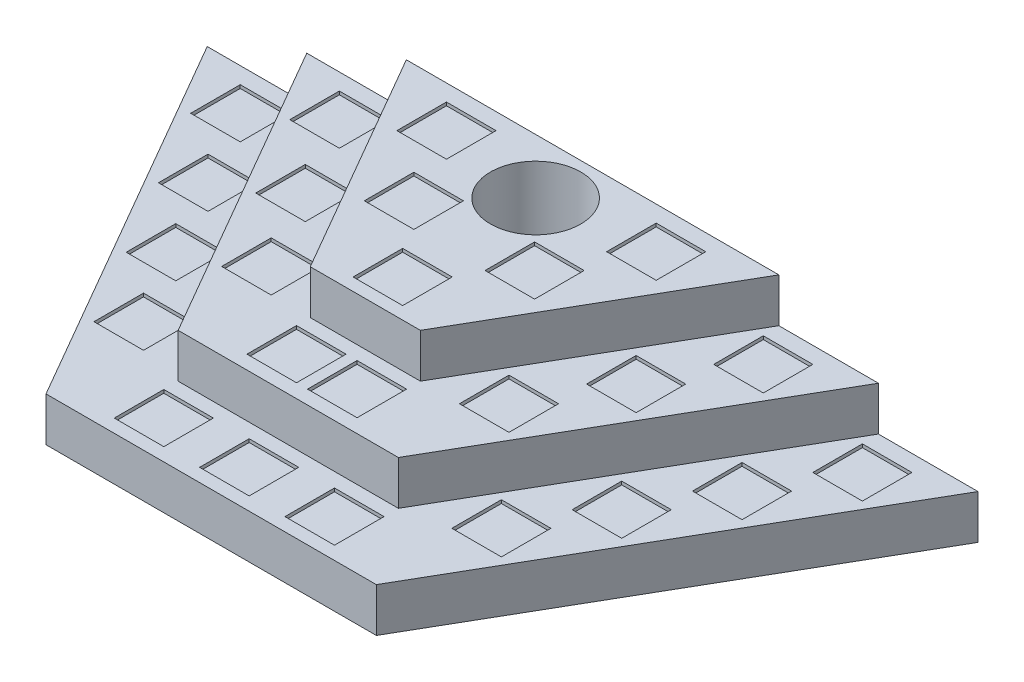
SolidWorks part; units mm, degrees
ref_plane "Front Plane" through (0, 0, 0) normal (0, 0, 1) x (1, 0, 0)
ref_plane "Top Plane" through (0, 0, 0) normal (0, 1, 0) x (1, 0, 0)
ref_plane "Right Plane" through (0, 0, 0) normal (1, 0, 0) x (0, 0, -1)
sketch "Sketch1" plane through (0, 0, 0) normal (0, 1, 0) x (1, 0, 0)
  line L0 (-150, 0) -> (150, 0)
  line L1 (150, 0) -> (350, 346.4102)
  line L2 (350, 346.4102) -> (-350, 346.4102)
  line L3 (-350, 346.4102) -> (-150, 0)
  point P4 (0, 0)
  dimension "D1" = 700
  dimension "D2" = 300
  dimension "D3" = 60
  dimension "D4" = 60
extrude "Boss-Extrude1" add sketch "Sketch1" along normal blind 40
sketch "Sketch3" plane through (0, 40, 0) normal (0, 1, 0) x (1, 0, 0)
  line L0 (-100, 70) -> (100, 70)
  line L1 (-150, 0) -> (150, 0) construction
  line L2 (-100, 70) -> (-259.5855, 346.4102)
  line L3 (350, 346.4102) -> (-350, 346.4102) construction
  line L4 (0, 0) -> (0, 370.2968) construction
  line L5 (100, 70) -> (259.5855, 346.4102)
  line L6 (-50, 140) -> (50, 140)
  line L7 (-50, 140) -> (-169.171, 346.4102)
  line L8 (50, 140) -> (169.171, 346.4102)
  line L9 (-259.5855, 346.4102) -> (-169.171, 346.4102)
  line L10 (259.5855, 346.4102) -> (169.171, 346.4102)
  point P5 (0, 70)
  point P14 (0, 140)
  dimension "D1" = 200
  dimension "D2" = 70
  dimension "D3" = 60
  dimension "D4" = 70
  dimension "D5" = 60
  dimension "D6" = 100
extrude "Boss-Extrude2" add sketch "Sketch3" along normal blind 40
sketch "Sketch4" plane through (0, 40, 0) normal (0, 1, 0) x (1, 0, 0)
  line L17 (-259.5855, 346.4102) -> (-100, 70)
  line L18 (-100, 70) -> (100, 70)
  line L19 (100, 70) -> (259.5855, 346.4102)
  line L20 (259.5855, 346.4102) -> (169.171, 346.4102)
  line L21 (169.171, 346.4102) -> (50, 140)
  line L22 (50, 140) -> (-50, 140)
  line L23 (-50, 140) -> (-169.171, 346.4102)
  line L24 (-169.171, 346.4102) -> (-259.5855, 346.4102)
  line L25 (-259.5855, 346.4102) -> (-100, 70)
  line L26 (-100, 70) -> (100, 70)
  line L27 (100, 70) -> (259.5855, 346.4102)
  line L28 (259.5855, 346.4102) -> (169.171, 346.4102)
  line L32 (169.171, 346.4102) -> (-259.5855, 346.4102)
  dimension "D2" = 0
extrude "Boss-Extrude3" add sketch "Sketch4" along normal blind 80
sketch "Sketch7" plane through (0, 40, 0) normal (0, 1, 0) x (1, 0, 0)
  line L0 (-150, 0) -> (150, 0) construction
  line L1 (-305, 331.4102) -> (-260, 331.4102)
  line L2 (-305, 331.4102) -> (-305, 286.4102)
  line L3 (-305, 286.4102) -> (-260, 286.4102)
  line L4 (-260, 331.4102) -> (-260, 286.4102)
  line L5 (-100, 57) -> (-55, 57)
  line L6 (-100, 57) -> (-100, 12)
  line L7 (-100, 12) -> (-55, 12)
  line L8 (-55, 57) -> (-55, 12)
  line L9 (-259.5855, 346.4102) -> (-350, 346.4102) construction
  line L10 (0, 0) -> (0, 441.8667) construction
  line L11 (-265, 262.1281) -> (-265, 217.1281)
  line L12 (-265, 262.1281) -> (-220, 262.1281)
  line L13 (-220, 262.1281) -> (-220, 217.1281)
  line L14 (-265, 217.1281) -> (-220, 217.1281)
  line L15 (-225, 192.8461) -> (-225, 147.8461)
  line L16 (-225, 192.8461) -> (-180, 192.8461)
  line L17 (-180, 192.8461) -> (-180, 147.8461)
  line L18 (-225, 147.8461) -> (-180, 147.8461)
  line L19 (-185, 123.5641) -> (-185, 78.5641)
  line L20 (-185, 123.5641) -> (-140, 123.5641)
  line L21 (-140, 123.5641) -> (-140, 78.5641)
  line L22 (-185, 78.5641) -> (-140, 78.5641)
  line L23 (305, 286.4102) -> (260, 286.4102)
  line L24 (260, 331.4102) -> (260, 286.4102)
  line L25 (305, 331.4102) -> (260, 331.4102)
  line L26 (305, 331.4102) -> (305, 286.4102)
  line L27 (185, 123.5641) -> (140, 123.5641)
  line L28 (140, 123.5641) -> (140, 78.5641)
  line L29 (185, 78.5641) -> (140, 78.5641)
  line L30 (185, 123.5641) -> (185, 78.5641)
  line L31 (225, 192.8461) -> (180, 192.8461)
  line L32 (180, 192.8461) -> (180, 147.8461)
  line L33 (225, 147.8461) -> (180, 147.8461)
  line L34 (225, 192.8461) -> (225, 147.8461)
  line L35 (265, 262.1281) -> (220, 262.1281)
  line L36 (220, 262.1281) -> (220, 217.1281)
  line L37 (265, 217.1281) -> (220, 217.1281)
  line L38 (265, 262.1281) -> (265, 217.1281)
  line L40 (-22.5, 57) -> (-22.5, 12)
  line L41 (-22.5, 57) -> (22.5, 57)
  line L42 (22.5, 57) -> (22.5, 12)
  line L43 (-22.5, 12) -> (22.5, 12)
  line L44 (55, 57) -> (55, 12)
  line L45 (55, 57) -> (100, 57)
  line L46 (100, 57) -> (100, 12)
  line L47 (55, 12) -> (100, 12)
  point P8 (-220, 239.6281)
  point P47 (0, 12)
  dimension "D1" = 45
  dimension "D2" = 45
  dimension "D3" = 60
  dimension "D4" = 260
  dimension "D6" = 220
  dimension "D7" = 12
  dimension "D8" = 100
  dimension "D5" = 4
  dimension "D9" = 3
extrude "Cut-Extrude2" cut sketch "Sketch7" against normal blind 3
sketch "Sketch8" plane through (0, 80, 0) normal (0, 1, 0) x (1, 0, 0)
  line L0 (-260, 331.4102) -> (-305, 331.4102) construction
  line L1 (-215, 331.4102) -> (-170, 331.4102)
  line L2 (-215, 331.4102) -> (-215, 286.4102)
  line L3 (-215, 286.4102) -> (-170, 286.4102)
  line L4 (-170, 331.4102) -> (-170, 286.4102)
  line L5 (-260, 331.4102) -> (-305, 331.4102) construction
  line L6 (0, 0) -> (0, 453.8323) construction
  line L7 (-172.735, 258.2051) -> (-172.735, 213.2051)
  line L8 (-172.735, 258.2051) -> (-127.735, 258.2051)
  line L9 (-127.735, 258.2051) -> (-127.735, 213.2051)
  line L10 (-172.735, 213.2051) -> (-127.735, 213.2051)
  line L11 (-130.4701, 185) -> (-130.4701, 140)
  line L12 (-130.4701, 185) -> (-85.4701, 185)
  line L13 (-85.4701, 185) -> (-85.4701, 140)
  line L14 (-130.4701, 140) -> (-85.4701, 140)
  line L15 (50, 140) -> (-50, 140) construction
  line L16 (215, 286.4102) -> (170, 286.4102)
  line L17 (170, 331.4102) -> (170, 286.4102)
  line L18 (215, 331.4102) -> (170, 331.4102)
  line L19 (215, 331.4102) -> (215, 286.4102)
  line L20 (172.735, 258.2051) -> (127.735, 258.2051)
  line L21 (127.735, 258.2051) -> (127.735, 213.2051)
  line L22 (172.735, 213.2051) -> (127.735, 213.2051)
  line L23 (172.735, 258.2051) -> (172.735, 213.2051)
  line L24 (130.4701, 185) -> (85.4701, 185)
  line L25 (85.4701, 185) -> (85.4701, 140)
  line L26 (130.4701, 140) -> (85.4701, 140)
  line L27 (130.4701, 185) -> (130.4701, 140)
  dimension "D1" = 170
  dimension "D2" = 3
extrude "Cut-Extrude3" cut sketch "Sketch8" against normal blind 3
sketch "Sketch9" plane through (0, 80, 0) normal (0, 1, 0) x (1, 0, 0)
  line L0 (-130.4701, 140) -> (-85.4701, 140) construction
  line L1 (-50, 127.5) -> (-5, 127.5)
  line L2 (-50, 127.5) -> (-50, 82.5)
  line L3 (-50, 82.5) -> (-5, 82.5)
  line L4 (-5, 127.5) -> (-5, 82.5)
  line L5 (50, 140) -> (-50, 140) construction
  line L7 (5, 127.5) -> (5, 82.5)
  line L8 (5, 127.5) -> (50, 127.5)
  line L9 (50, 127.5) -> (50, 82.5)
  line L10 (5, 82.5) -> (50, 82.5)
  dimension "D1" = 12.5
  dimension "D2" = 2
extrude "Cut-Extrude4" cut sketch "Sketch9" against normal blind 3
sketch "Sketch11" plane through (0, 120, 0) normal (0, 1, 0) x (1, 0, 0)
  line L0 (0, 0) -> (0, 385.805) construction
  line L1 (-77.3205, 261.4102) -> (-77.3205, 216.4102)
  line L2 (-117.735, 331.4102) -> (-72.735, 331.4102)
  line L3 (-117.735, 331.4102) -> (-117.735, 286.4102)
  line L4 (-117.735, 286.4102) -> (-72.735, 286.4102)
  line L5 (-72.735, 331.4102) -> (-72.735, 286.4102)
  line L6 (-77.3205, 261.4102) -> (-32.3205, 261.4102)
  line L7 (-32.3205, 261.4102) -> (-32.3205, 216.4102)
  line L8 (-77.3205, 216.4102) -> (-32.3205, 216.4102)
  line L9 (77.3205, 261.4102) -> (32.3205, 261.4102)
  line L10 (-170, 331.4102) -> (-215, 331.4102) construction
  line L11 (32.3205, 261.4102) -> (32.3205, 216.4102)
  line L12 (77.3205, 216.4102) -> (32.3205, 216.4102)
  line L13 (77.3205, 261.4102) -> (77.3205, 216.4102)
  line L14 (117.735, 286.4102) -> (72.735, 286.4102)
  line L15 (72.735, 331.4102) -> (72.735, 286.4102)
  line L16 (117.735, 331.4102) -> (72.735, 331.4102)
  line L17 (117.735, 331.4102) -> (117.735, 286.4102)
  line L19 (-22.5, 196.4102) -> (22.5, 196.4102)
  line L20 (-22.5, 196.4102) -> (-22.5, 151.4102)
  line L21 (-22.5, 151.4102) -> (22.5, 151.4102)
  line L22 (22.5, 196.4102) -> (22.5, 151.4102)
  line L23 (-127.735, 213.2051) -> (-127.735, 258.2051) construction
  point P13 (0, 196.4102)
  dimension "D1" = 45
  dimension "D3" = 10
  dimension "D4" = 25
  dimension "D5" = 20
  dimension "D2" = 2
extrude "Cut-Extrude5" cut sketch "Sketch11" against normal blind 3
sketch "Sketch13" plane through (0, 120, 0) normal (0, 1, 0) x (1, 0, 0)
  line L0 (169.171, 346.4102) -> (-169.171, 346.4102) construction
  line L1 (-72.735, 286.4102) -> (-72.735, 331.4102) construction
  circle A0 centre (-1.735, 296.4102) radius 41
  dimension "D1" = 82
  dimension "D3" = 71
  dimension "D2" = 50
extrude "Cut-Extrude6" cut sketch "Sketch13" against normal offset from surface (117 mm away) 3 up to face at (0, 0, -173.2051)
